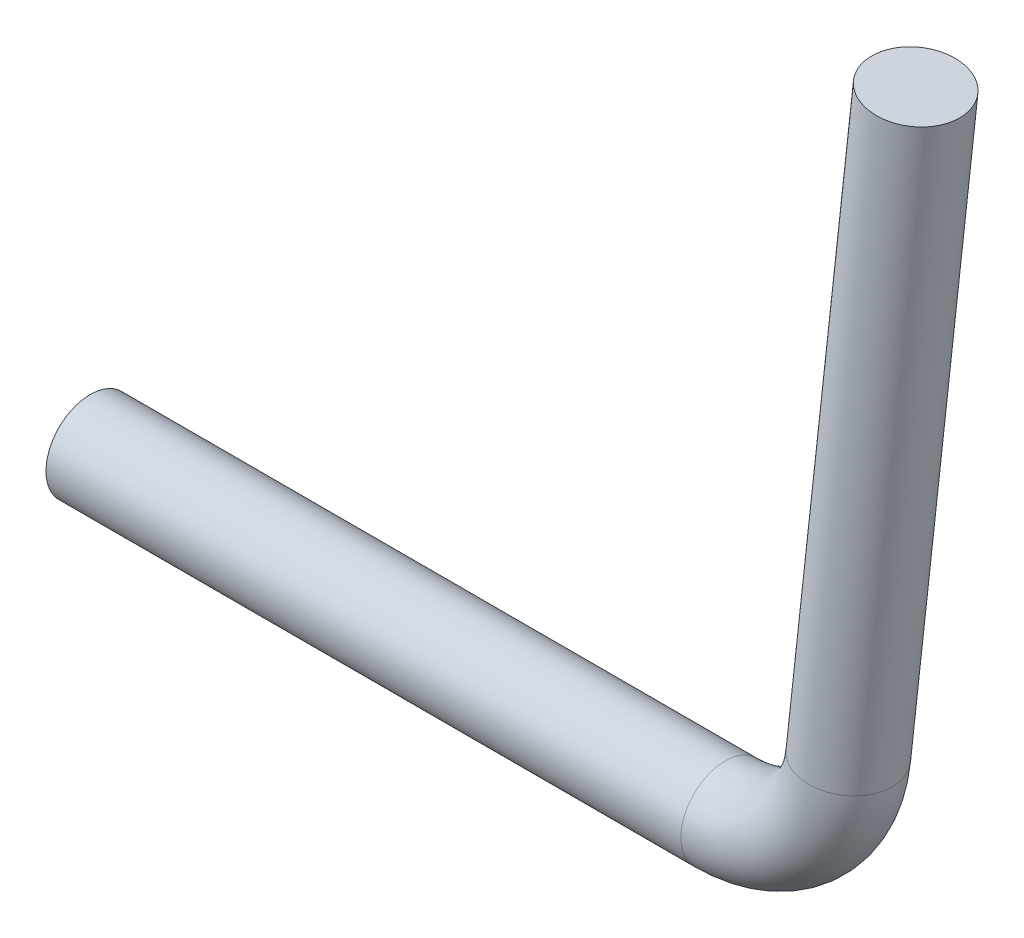
SolidWorks part; units mm, degrees
ref_plane "Спереди" through (0, 0, 0) normal (0, 0, 1) x (1, 0, 0)
ref_plane "Сверху" through (0, 0, 0) normal (0, 1, 0) x (1, 0, 0)
ref_plane "Справа" through (0, 0, 0) normal (1, 0, 0) x (0, 0, -1)
other "Configuration Table"
sketch "Sketch1" plane through (0, 0, 0) normal (0, 0, 1) x (1, 0, 0)
  line L0 (-31.808, 9.6116) -> (4.0605, 9.6116)
  line L1 (14.8299, 50.48) -> (11.0185, 15.8459)
  arc A0 (4.0605, 9.6116) -> (11.0185, 15.8459) centre (4.0605, 16.6116) ccw
  point P2 (0, 0)
  point P6 (0, 0)
  dimension "D1" = 7
sweep "Sweep2" add path "Sketch1" circular profile diameter 5 parameters "D3"=5
